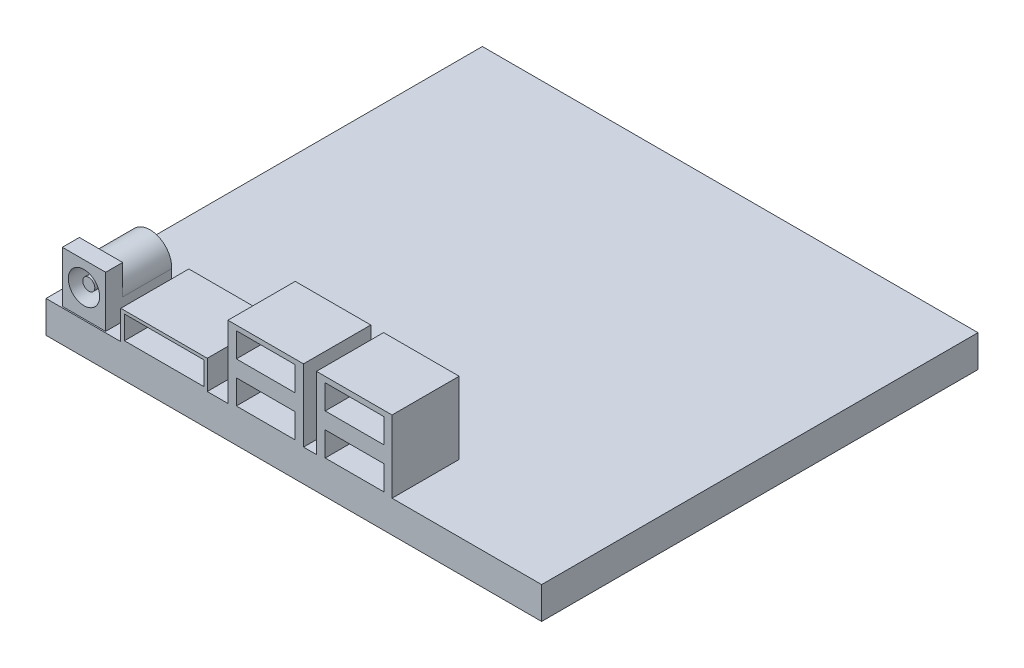
SolidWorks part; units mm, degrees
ref_plane "Front Plane" through (0, 0, 0) normal (0, 0, 1) x (1, 0, 0)
ref_plane "Top Plane" through (0, 0, 0) normal (0, 1, 0) x (1, 0, 0)
ref_plane "Right Plane" through (0, 0, 0) normal (1, 0, 0) x (0, 0, -1)
sketch "Sketch1" plane through (0, 0, 0) normal (0, 1, 0) x (1, 0, 0)
  line L1 (51.555, -45.39) -> (-51.555, -45.39)
  line L2 (51.555, -45.39) -> (51.555, 45.39)
  line L3 (51.555, 45.39) -> (-51.555, 45.39)
  line L4 (-51.555, -45.39) -> (-51.555, 45.39)
  line L5 (51.555, -45.39) -> (-51.555, 45.39) construction
  line L6 (51.555, 45.39) -> (-51.555, -45.39) construction
  point P0 (0, 0)
  dimension "D1" = 90.78
  dimension "D2" = 103.11
extrude "Boss-Extrude1" add sketch "Sketch1" along normal blind 6.65
sketch "Sketch2" plane through (0, 6.65, 0) normal (0, 1, 0) x (1, 0, 0)
  line L0 (-51.555, 45.39) -> (-51.555, -45.39) construction
  line L1 (-48.425, -45.1202) -> (-39.415, -45.1202)
  line L2 (-48.425, -45.1202) -> (-48.425, -41.5802)
  line L3 (-48.425, -41.5802) -> (-39.415, -41.5802)
  line L4 (-39.415, -45.1202) -> (-39.415, -41.5802)
  line L5 (-48.425, -45.1202) -> (-39.415, -41.5802) construction
  line L6 (-48.425, -41.5802) -> (-39.415, -45.1202) construction
  point P0 (-43.92, -43.3502)
  dimension "D1" = 3.54
  dimension "D2" = 9.01
  dimension "D3" = 3.13
extrude "Boss-Extrude2" add sketch "Sketch2" along normal blind 10.65
sketch "Sketch3" plane through (0, 0, 41.5802) normal (0, 0, -1) x (-1, 0, 0)
  line L4 (39.415, 6.65) -> (39.415, 11.0782)
  line L5 (39.415, 17.3) -> (39.415, 6.65) construction
  line L6 (48.425, 17.3) -> (48.425, 6.65) construction
  line L7 (39.415, 6.65) -> (48.425, 6.65)
  line L8 (39.415, 6.65) -> (48.425, 6.65) construction
  line L9 (48.425, 6.65) -> (48.425, 11.0782)
  arc A0 (39.415, 11.0782) -> (48.425, 11.0782) centre (43.92, 11.3432) cw
extrude "Boss-Extrude3" add sketch "Sketch3" along normal blind 10.18
sketch "Sketch4" plane through (0, 0, 45.1202) normal (0, 0, 1) x (1, 0, 0)
  line L0 (-48.425, 17.3) -> (-48.425, 6.65) construction
  circle A0 centre (-43.925, 12.2861) radius 3.26
  dimension "D1" = 6.52
  dimension "D2" = 4.5
extrude "Cut-Extrude1" cut sketch "Sketch4" against normal blind 10.18
sketch "Sketch6" plane through (0, 0, 34.9402) normal (0, 0, 1) x (1, 0, 0)
  circle A0 centre (-43.9259, 12.3768) radius 1.25
  dimension "D1" = 2.5
extrude "Boss-Extrude4" add sketch "Sketch6" along normal blind 9.18
sketch "Sketch7" plane through (0, 6.65, 0) normal (0, 1, 0) x (1, 0, 0)
  line L0 (-39.4072, -41.5802) -> (-39.4072, -31.4002) construction
  line L2 (-36.0072, -31.22) -> (-36.0072, -45.39)
  line L3 (-36.0072, -45.39) -> (-18.0072, -45.39)
  line L4 (-18.0072, -30.297) -> (-18.0072, -45.39)
  line L5 (-36.0072, -31.22) -> (-18.0072, -45.39) construction
  line L6 (-36.0072, -45.39) -> (-18.0072, -30.297) construction
  line L7 (-51.555, -45.39) -> (51.555, -45.39) construction
  line L8 (-36.0072, -31.22) -> (-18.0072, -31.22)
  point P0 (-27.2911, -38.0815)
  line M7 (-51.555, -45.39) -> (51.555, -45.39)
  dimension "D1" = 3.4
  dimension "D2" = 0
  dimension "D3" = 14.17
  dimension "D4" = 18
extrude "Boss-Extrude5" add sketch "Sketch7" along normal blind 6 contours L8 L2 L4 M7
sketch "Sketch8" plane through (0, 0, 45.39) normal (0, 0, 1) x (1, 0, 0)
  line L1 (-18.7326, 7.1878) -> (-35.2326, 7.1878)
  line L2 (-18.7326, 7.1878) -> (-18.7326, 12.0078)
  line L3 (-18.7326, 12.0078) -> (-35.2326, 12.0078)
  line L4 (-35.2326, 7.1878) -> (-35.2326, 12.0078)
  line L5 (-18.7326, 7.1878) -> (-35.2326, 12.0078) construction
  line L6 (-18.7326, 12.0078) -> (-35.2326, 7.1878) construction
  point P0 (-26.9826, 9.5978)
  point P5 (-26.9826, 9.5978)
  dimension "D1" = 16.5
extrude "Cut-Extrude2" cut sketch "Sketch8" against normal blind 9
sketch "Sketch9" plane through (0, 6.65, 0) normal (0, 1, 0) x (1, 0, 0)
  line L0 (-18.0072, -45.39) -> (51.555, -45.39) construction
  line L1 (-13.7072, -45.39) -> (2.0128, -45.39)
  line L2 (-13.7072, -45.39) -> (-13.7072, -31.39)
  line L3 (-13.7072, -31.39) -> (2.0128, -31.39)
  line L4 (2.0128, -45.39) -> (2.0128, -31.39)
  line L5 (-13.7072, -45.39) -> (2.0128, -45.39)
  line L6 (-18.0072, -31.22) -> (-18.0072, -45.39) construction
  line M11 (-18.0072, -45.39) -> (51.555, -45.39)
  dimension "D1" = 14
  dimension "D2" = 15.72
  dimension "D3" = 4.3
extrude "Boss-Extrude6" add sketch "Sketch9" along normal blind 15 contours L4 L3 L2 M11
sketch "Sketch10" plane through (0, 0, 45.39) normal (0, 0, 1) x (1, 0, 0)
  line L1 (-11.9563, 15.5557) -> (0.2937, 15.5557)
  line L2 (-11.9563, 15.5557) -> (-11.9563, 20.6357)
  line L3 (-11.9563, 20.6357) -> (0.2937, 20.6357)
  line L4 (0.2937, 15.5557) -> (0.2937, 20.6357)
  line L9 (-11.9563, 7.0755) -> (0.2937, 7.0755)
  line L10 (-11.9563, 7.0755) -> (-11.9563, 12.1555)
  line L11 (-11.9563, 12.1555) -> (0.2937, 12.1555)
  line L12 (0.2937, 7.0755) -> (0.2937, 12.1555)
  dimension "D1" = 12.25
  dimension "D2" = 5.08
  dimension "D3" = 5.08
extrude "Cut-Extrude3" cut sketch "Sketch10" against normal blind 7.5
sketch "Sketch11" plane through (0, 0, 0) normal (0, 0, 1) x (1, 0, 0)
  line L1 (-13.7072, -45.39) -> (2.0128, -45.39)
  line L2 (-13.7072, -45.39) -> (-13.7072, -31.39)
  line L3 (-13.7072, -31.39) -> (2.0128, -31.39)
  line L4 (2.0128, -45.39) -> (2.0128, -31.39)
  line L5 (-13.7072, -45.39) -> (2.0128, -45.39)
  dimension "D1" = 14
  dimension "D2" = 15.72
sketch "Sketch12" plane through (0, 6.65, 0) normal (0, 1, 0) x (1, 0, 0)
  line L0 (4.7128, -45.4259) -> (20.4328, -45.4259)
  line L1 (4.7128, -45.4259) -> (4.7128, -31.4259)
  line L2 (4.7128, -31.4259) -> (20.4328, -31.4259)
  line L3 (20.4328, -45.4259) -> (20.4328, -31.4259)
  line L4 (4.7128, -45.4259) -> (20.4328, -45.4259)
  line L5 (2.0128, -45.39) -> (2.0128, -31.39) construction
  line M9 (2.0128, -45.39) -> (51.555, -45.39)
  dimension "D1" = 2.7
extrude "Boss-Extrude7" add sketch "Sketch12" along normal blind 15 contours L3 L2 L1 M9
sketch "Sketch13" plane through (0, 0, 45.39) normal (0, 0, 1) x (1, 0, 0)
  line L0 (6.5317, 15.4229) -> (18.7817, 15.4229)
  line L1 (6.5317, 15.4229) -> (6.5317, 20.5029)
  line L2 (6.5317, 20.5029) -> (18.7817, 20.5029)
  line L3 (18.7817, 15.4229) -> (18.7817, 20.5029)
  line L4 (6.5317, 6.9427) -> (18.7817, 6.9427)
  line L5 (6.5317, 6.9427) -> (6.5317, 12.0227)
  line L6 (6.5317, 12.0227) -> (18.7817, 12.0227)
  line L7 (18.7817, 6.9427) -> (18.7817, 12.0227)
extrude "Cut-Extrude4" cut sketch "Sketch13" against normal blind 7.5
